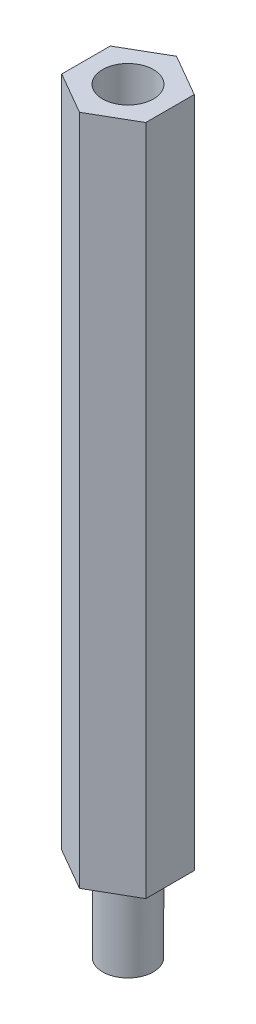
SolidWorks part; units mm, degrees
ref_plane "Front Plane" through (0, 0, 0) normal (0, 0, 1) x (1, 0, 0)
ref_plane "Top Plane" through (0, 0, 0) normal (0, 1, 0) x (1, 0, 0)
ref_plane "Right Plane" through (0, 0, 0) normal (1, 0, 0) x (0, 0, -1)
sketch "Sketch1" plane through (0, 0, 0) normal (0, 1, 0) x (1, 0, 0)
  line L1 (0, -2.8868) -> (2.5, -1.4434)
  line L2 (2.5, -1.4434) -> (2.5, 1.4434)
  line L3 (2.5, 1.4434) -> (0, 2.8868)
  line L4 (0, 2.8868) -> (-2.5, 1.4434)
  line L5 (-2.5, 1.4434) -> (-2.5, -1.4434)
  line L6 (-2.5, -1.4434) -> (0, -2.8868)
  circle A0 centre (0, 0) radius 2.5 construction
extrude "Boss-Extrude1" add sketch "Sketch1" along normal blind 40
sketch "Sketch2" plane through (0, 40, 0) normal (0, 1, 0) x (1, 0, 0)
  circle A0 centre (0, 0) radius 1.5161
extrude "Cut-Extrude1" cut sketch "Sketch2" against normal blind 10
sketch "Sketch3" plane through (0, 0, 0) normal (0, -1, 0) x (1, 0, 0)
  circle A0 centre (0, 0) radius 1.5059
extrude "Boss-Extrude2" add sketch "Sketch3" along normal blind 5
